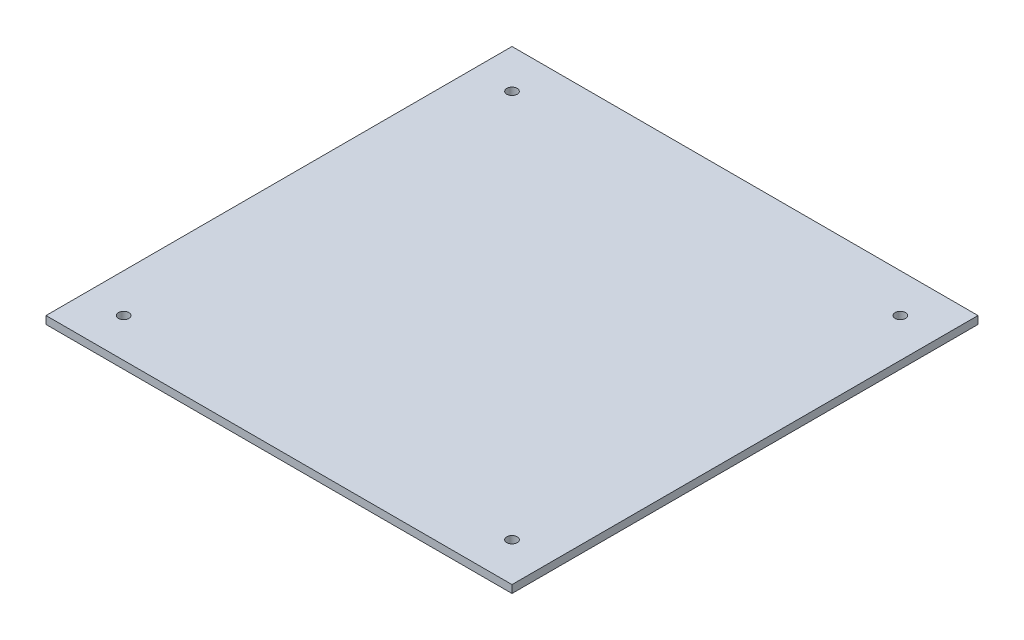
SolidWorks part; units mm, degrees
ref_plane "Front Plane" through (0, 0, 0) normal (0, 0, 1) x (1, 0, 0)
ref_plane "Top Plane" through (0, 0, 0) normal (0, 1, 0) x (1, 0, 0)
ref_plane "Right Plane" through (0, 0, 0) normal (1, 0, 0) x (0, 0, -1)
sketch "Sketch1" plane through (0, 0, 0) normal (0, 1, 0) x (1, 0, 0)
  line L1 (90, -90) -> (-90, -90)
  line L2 (90, -90) -> (90, 90)
  line L3 (90, 90) -> (-90, 90)
  line L4 (-90, -90) -> (-90, 90)
  line L5 (90, -90) -> (-90, 90) construction
  line L6 (90, 90) -> (-90, -90) construction
  circle A0 centre (-75, 75) radius 2
  circle A1 centre (75, 75) radius 2
  circle A2 centre (-75, -75) radius 2
  circle A3 centre (75, -75) radius 2
  point P0 (0, 0)
  dimension "D3" = 4
  dimension "D4" = 4
  dimension "D5" = 4
  dimension "D6" = 4
  dimension "D1" = 180
  dimension "D2" = 180
  dimension "D7" = 15
  dimension "D8" = 15
  dimension "D9" = 15
  dimension "D10" = 15
extrude "Boss-Extrude1" add sketch "Sketch1" along normal blind 3
